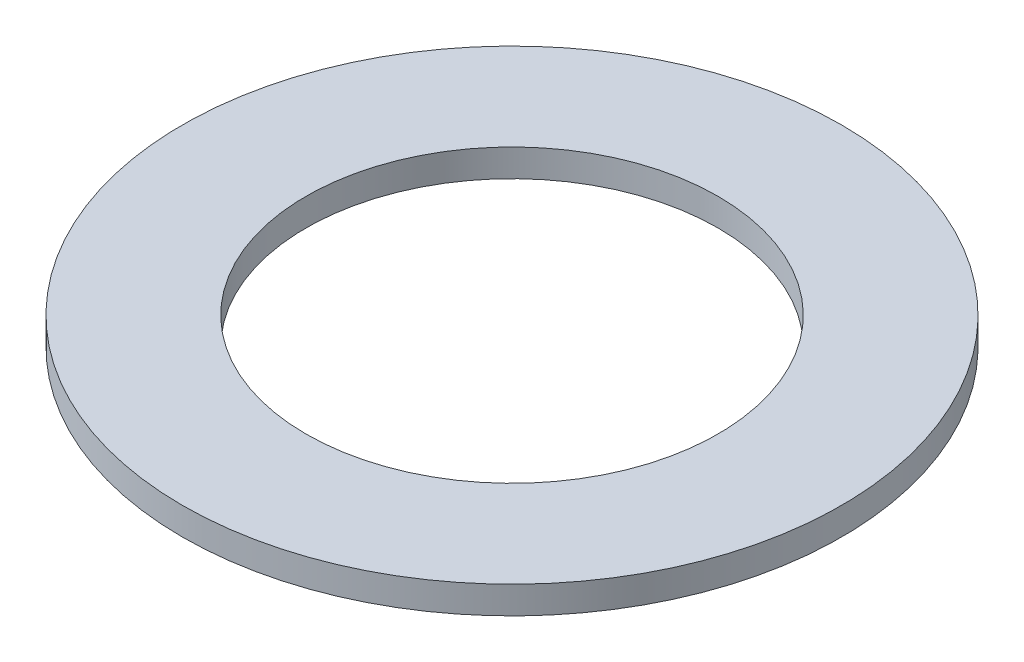
SolidWorks part; units mm, degrees
ref_plane "Front Plane" through (0, 0, 0) normal (0, 0, 1) x (1, 0, 0)
ref_plane "Top Plane" through (0, 0, 0) normal (0, 1, 0) x (1, 0, 0)
ref_plane "Right Plane" through (0, 0, 0) normal (1, 0, 0) x (0, 0, -1)
sketch "Sketch1" plane through (0, 0, 0) normal (0, 1, 0) x (1, 0, 0)
  circle A0 centre (0, 0) radius 7.5
  circle A1 centre (0, 0) radius 12
  dimension "D1" = 15
  dimension "D2" = 24
extrude "PDMS Gasket" add sketch "Sketch1" along normal blind 1
